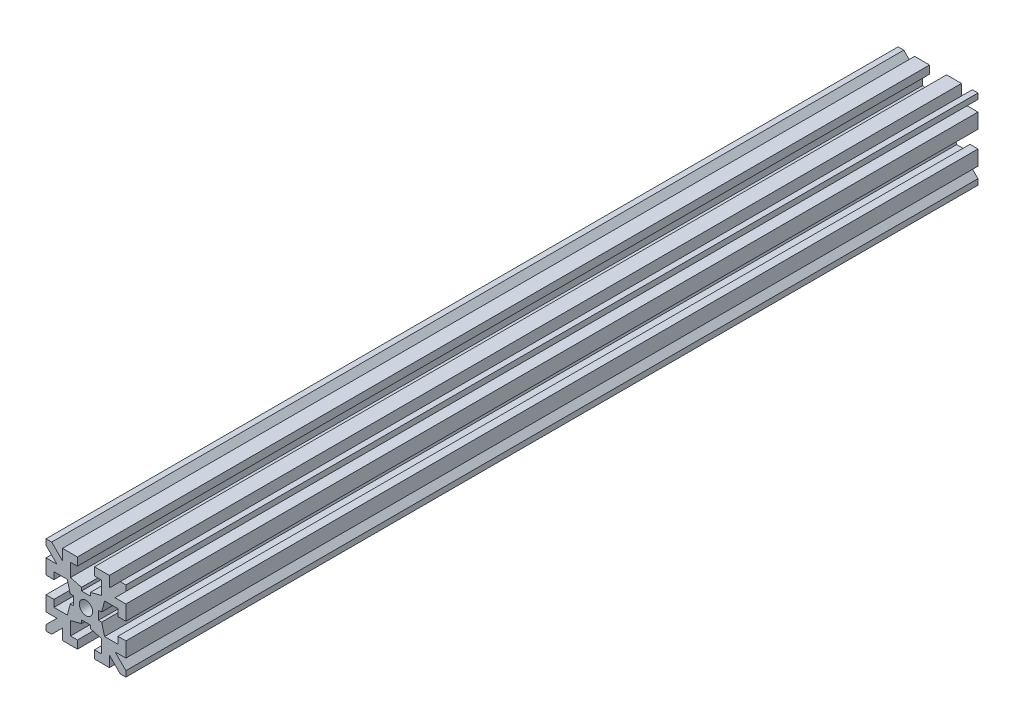
SolidWorks part; units mm, degrees
material "3.0205 (EN-AW 1200)"
ref_plane "Plano frontal" through (0, 0, 0) normal (0, 0, 1) x (1, 0, 0)
ref_plane "Plano superior" through (0, 0, 0) normal (0, 1, 0) x (1, 0, 0)
ref_plane "Plano direito" through (0, 0, 0) normal (1, 0, 0) x (0, 0, -1)
sketch "Esboço1" plane through (0, 0, 0) normal (0, 0, 1) x (1, 0, 0)
  line L0 (-25.7554, 0) -> (0, 0) construction
  line L1 (0, 0) -> (0, 21.5914) construction
  line L2 (0, 2.35) -> (-0.825, 2.35)
  line L3 (-0.825, 2.35) -> (-0.825, 2.95)
  line L4 (-0.825, 2.95) -> (-2.9, 3.5)
  line L5 (-2.9, 3.5) -> (-2.9, 6)
  line L6 (-2.9, 6) -> (-1.6, 6)
  line L7 (-1.6, 6) -> (-1.6, 7.5)
  line L8 (-1.6, 7.5) -> (-4.4, 7.5)
  line L9 (-4.4, 7.5) -> (-4.4, 5.4607)
  line L10 (-4.4, 5.4607) -> (-6.4393, 7.5)
  line L11 (-6.4393, 7.5) -> (-7.5, 7.5)
  line L12 (-7.5, 7.5) -> (0, 0) construction
  line L13 (-2.35, 0) -> (-2.35, 0.825)
  line L14 (-7.5, 6.4393) -> (-7.5, 7.5)
  line L15 (-5.4607, 4.4) -> (-7.5, 6.4393)
  line L16 (-7.5, 4.4) -> (-5.4607, 4.4)
  line L17 (-7.5, 1.6) -> (-7.5, 4.4)
  line L18 (-6, 1.6) -> (-7.5, 1.6)
  line L19 (-6, 2.9) -> (-6, 1.6)
  line L20 (-3.5, 2.9) -> (-6, 2.9)
  line L21 (-2.95, 0.825) -> (-3.5, 2.9)
  line L22 (-2.35, 0.825) -> (-2.95, 0.825)
  line L23 (-2.35, 0) -> (0, 0)
  line L24 (0, 0) -> (0, 2.35)
  dimension "D1" = 45
  dimension "D2" = 4.7
  dimension "D3" = 5.8
  dimension "D4" = 15
  dimension "D5" = 3.1
  dimension "D6" = 3.2
  dimension "D7" = 0.6
  dimension "D8" = 1.65
  dimension "D9" = 1.5
  dimension "D10" = 2.5
  dimension "D11" = 1.5
extrude "Ressalto-extrusão1" add sketch "Esboço1" along normal mid plane 160
mirror "Espelhar1" about plane through (0, 0, 0) normal (0, 1, 0) of "Ressalto-extrusão1"
mirror "Espelhar2" about plane through (0, 0, 0) normal (1, 0, 0) of "Espelhar1", "Ressalto-extrusão1"
sketch "Esboço2" plane through (0, 0, 80) normal (0, 0, 1) x (1, 0, 0)
  circle A0 centre (0, 0) radius 1.25
  dimension "D1" = 2.5
extrude "Corte-extrusão1" cut sketch "Esboço2" against normal through all both and the other way through all
